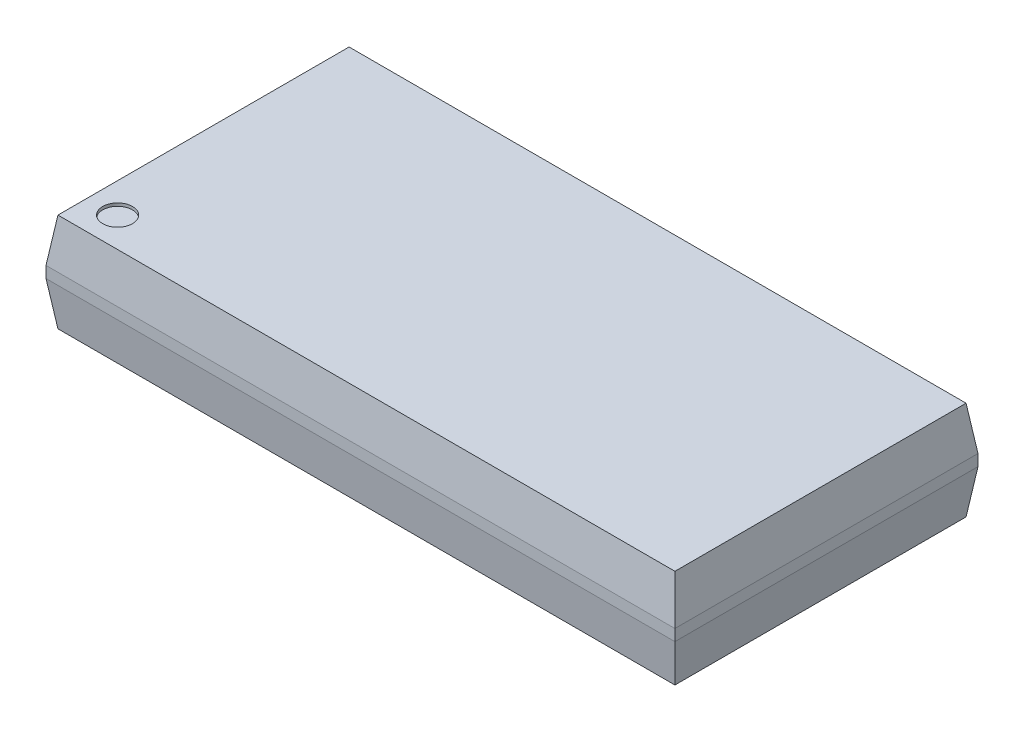
SolidWorks part; units mm, degrees
ref_plane "Front Plane" through (0, 0, 0) normal (0, 0, 1) x (1, 0, 0)
ref_plane "Top Plane" through (0, 0, 0) normal (0, 1, 0) x (1, 0, 0)
ref_plane "Right Plane" through (0, 0, 0) normal (1, 0, 0) x (0, 0, -1)
sketch "Sketch1" plane through (0, 0, 0) normal (0, 1, 0) x (1, 0, 0)
  line L1 (-10.541, -5.08) -> (10.541, -5.08)
  line L2 (-10.541, -5.08) -> (-10.541, 5.08)
  line L3 (-10.541, 5.08) -> (10.541, 5.08)
  line L4 (10.541, -5.08) -> (10.541, 5.08)
  line L5 (-10.541, -5.08) -> (10.541, 5.08) construction
  line L6 (-10.541, 5.08) -> (10.541, -5.08) construction
  point P0 (0, 0)
  dimension "D1" = 21.082
  dimension "D2" = 10.16
extrude "Boss-Extrude1" add sketch "Sketch1" along normal mid plane 3.302
sketch "Sketch2" plane through (10.541, 0, 0) normal (1, 0, 0) x (0, 0, -1)
  line L0 (-5.08, 1.651) -> (-4.88, 1.651)
  line L1 (-5.08, 1.651) -> (5.08, 1.651) construction
  line L2 (-4.88, 1.651) -> (-5.08, 0.1905)
  line L3 (-5.08, 1.651) -> (-5.08, -1.651) construction
  line L4 (-5.08, 0.1905) -> (-5.08, 1.651)
  line L5 (5.588, 0) -> (-5.588, 0) construction
  dimension "D1" = 0.1905
  dimension "D2" = 0.2
extrude "Cut-Extrude1" cut sketch "Sketch2" against normal through all
mirror "Mirror1" about plane through (0, 0, 0) normal (0, 0, 1) of "Cut-Extrude1"
mirror "Mirror2" about plane through (0, 0, 0) normal (0, 1, 0) of "Mirror1", "Cut-Extrude1"
sketch "Sketch3" plane through (0, 0, 5.08) normal (0, 0, 1) x (1, 0, 0)
  line L0 (10.541, 0.1905) -> (10.541, 1.651)
  line L1 (10.541, 1.651) -> (10.341, 1.651)
  line L2 (-10.541, 1.651) -> (10.541, 1.651) construction
  line L3 (10.341, 1.651) -> (10.541, 0.1905)
  dimension "D1" = 0.2
extrude "Cut-Extrude2" cut sketch "Sketch3" against normal through all
mirror "Mirror3" about plane through (0, 0, 0) normal (0, 1, 0) of "Cut-Extrude2"
mirror "Mirror4" about plane through (0, 0, 0) normal (1, 0, 0) of "Mirror3", "Cut-Extrude2"
sketch "Sketch4" plane through (0, 1.651, 0) normal (0, 1, 0) x (1, 0, 0)
  line L0 (-10.341, -4.88) -> (10.341, -4.88) construction
  line L1 (-10.341, 4.88) -> (-10.341, -4.88) construction
  circle A0 centre (-9.341, -3.88) radius 0.5
  dimension "D1" = 1
  dimension "D2" = 1
  dimension "D3" = 1
extrude "Cut-Extrude3" cut sketch "Sketch4" against normal blind 0.1
